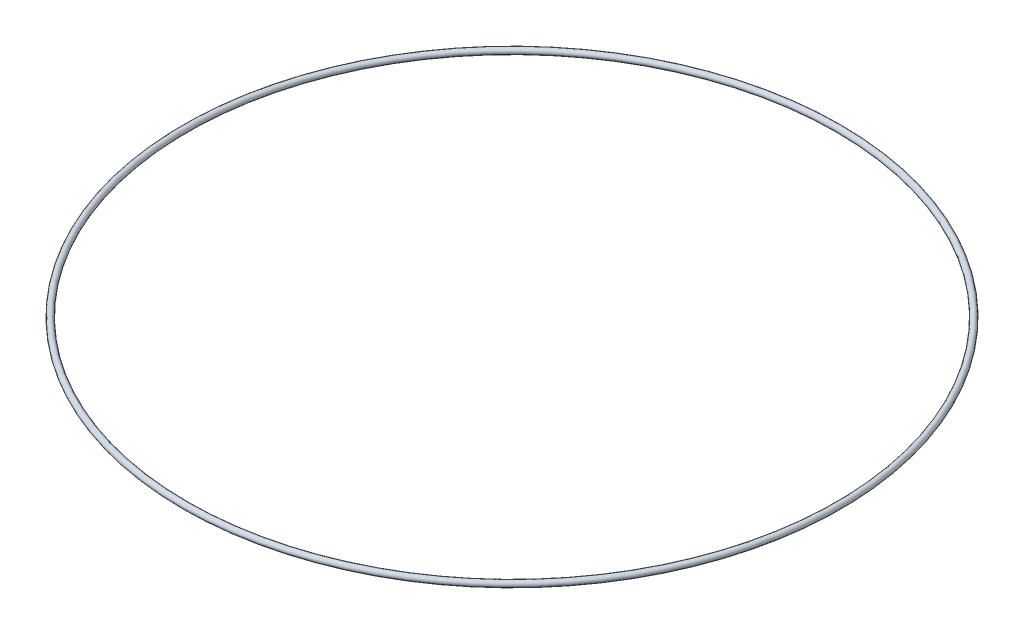
SolidWorks part; units mm, degrees
ref_plane "Front Plane" through (0, 0, 0) normal (0, 0, 1) x (1, 0, 0)
ref_plane "Top Plane" through (0, 0, 0) normal (0, 1, 0) x (1, 0, 0)
ref_plane "Right Plane" through (0, 0, 0) normal (1, 0, 0) x (0, 0, -1)
sketch "Sketch1" plane through (0, 0, 0) normal (0, 0, 1) x (1, 0, 0)
  line L0 (0, 0) -> (0, 26.6398) construction
  circle A0 centre (96.52, 0) radius 0.889
  point P2 (95.631, 0)
  dimension "D1" = 1.778
  dimension "D2" = 95.631
revolve "Revolve1" add sketch "Sketch1" angle 360 about L0
